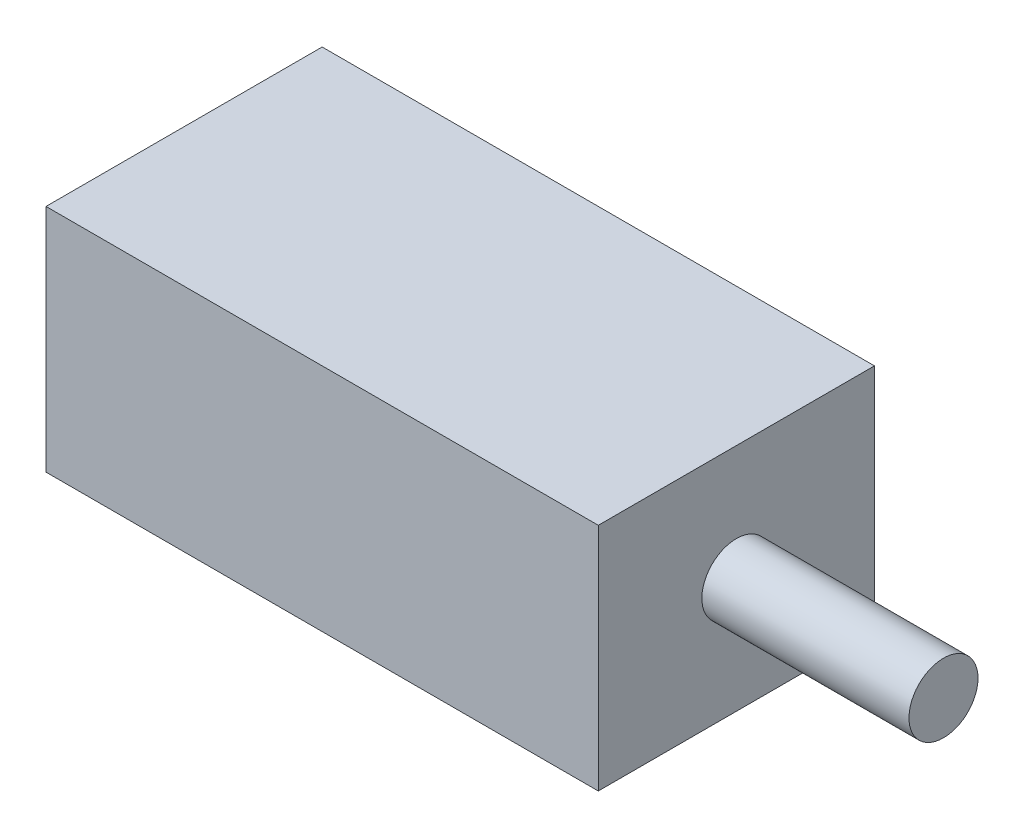
SolidWorks part; units mm, degrees
ref_plane "Ön Düzlem" through (0, 0, 0) normal (0, 0, 1) x (1, 0, 0)
ref_plane "Üst Düzlem" through (0, 0, 0) normal (0, 1, 0) x (1, 0, 0)
ref_plane "Sağ Düzlem" through (0, 0, 0) normal (1, 0, 0) x (0, 0, -1)
sketch "Sketch1" plane through (0, 0, 0) normal (0, 0, 1) x (1, 0, 0)
  line L1 (-12, 5) -> (12, 5)
  line L2 (-12, 5) -> (-12, -5)
  line L3 (-12, -5) -> (12, -5)
  line L4 (12, 5) -> (12, -5)
  line L5 (-12, 5) -> (12, -5) construction
  line L6 (-12, -5) -> (12, 5) construction
  point P0 (0, 0)
  dimension "D1" = 24
  dimension "D2" = 10
extrude "Boss-Extrude1" add sketch "Sketch1" along normal mid plane 12
sketch "Sketch2" plane through (0, 0, 0) normal (1, 0, 0) x (0, 0, -1)
  circle A0 centre (0, 0) radius 1.5
  dimension "D1" = 3
extrude "Boss-Extrude2" add sketch "Sketch2" along normal blind 21
